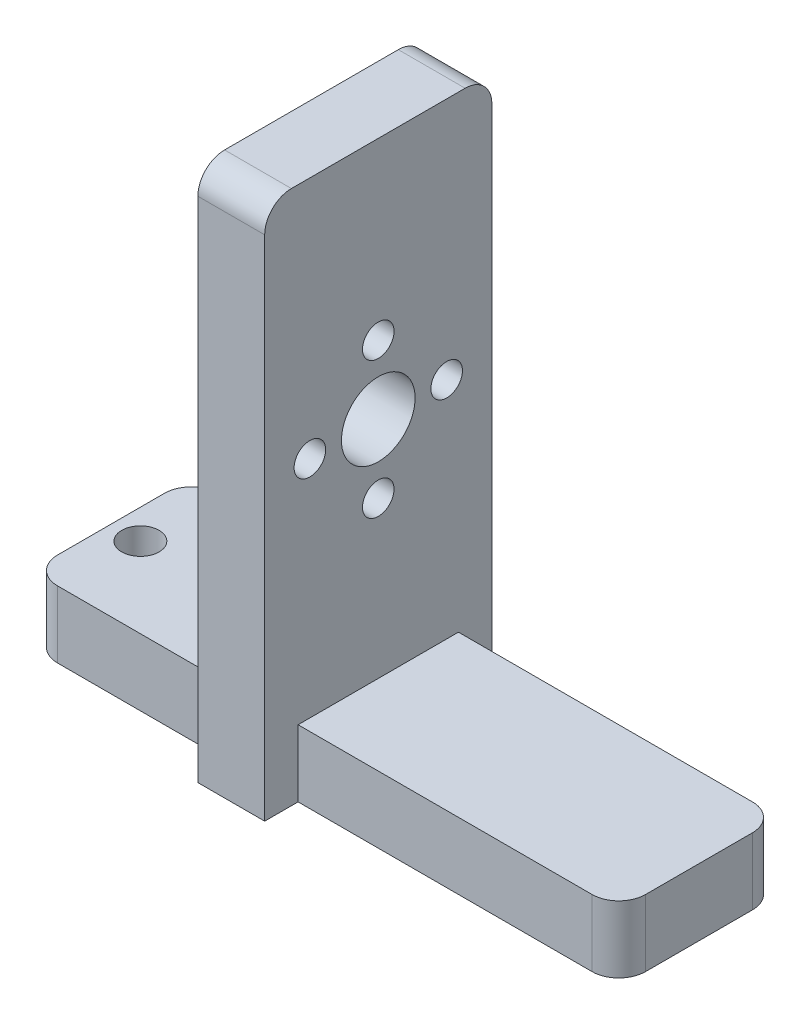
SolidWorks part; units mm, degrees
ref_plane "Front Plane" through (0, 0, 0) normal (0, 0, 1) x (1, 0, 0)
ref_plane "Top Plane" through (0, 0, 0) normal (0, 1, 0) x (1, 0, 0)
ref_plane "Right Plane" through (0, 0, 0) normal (1, 0, 0) x (0, 0, -1)
sketch "Sketch2" plane through (0, 0, 0) normal (0, 0, 1) x (1, 0, 0)
  line L0 (-27.94, 0) -> (27.94, 0)
  line L1 (27.94, 0) -> (27.94, 6.35)
  line L2 (27.94, 6.35) -> (-2.54, 6.35)
  line L3 (-2.54, 6.35) -> (-2.54, 50.8)
  line L4 (-2.54, 50.8) -> (-8.89, 50.8)
  line L5 (-8.89, 50.8) -> (-8.89, 6.35)
  line L6 (-8.89, 6.35) -> (-27.94, 6.35)
  line L7 (-27.94, 6.35) -> (-27.94, 0)
  dimension "D1" = 30.48
  dimension "D2" = 6.35
  dimension "D3" = 44.45
  dimension "D4" = 44.45
  dimension "D5" = 19.05
  dimension "D6" = 6.35
extrude "Boss-Extrude1" add sketch "Sketch2" along normal blind 15.24
sketch "Sketch5" plane through (-8.89, 0, 0) normal (-1, 0, 0) x (0, 0, 1)
  line L1 (15.24, 50.8) -> (0, 50.8) construction
  line L2 (0, 50.8) -> (0, 6.35) construction
  circle A1 centre (7.62, 27.686) radius 3.5
  dimension "D4" = 7
  dimension "D1" = 23.114
  dimension "D5" = 7.62
extrude "Cut-Extrude1" cut sketch "Sketch5" against normal blind 15.24
sketch "Sketch6" plane through (0, 6.35, 0) normal (0, 1, 0) x (1, 0, 0)
  line L0 (-8.89, 0) -> (-27.94, 0) construction
  line L1 (-27.94, -15.24) -> (-27.94, 0) construction
  circle A0 centre (-25.146, -7.62) radius 1.778
  circle A1 centre (-15.24, -7.62) radius 1.778
  dimension "D1" = 3.556
  dimension "D3" = 3.556
  dimension "D2" = 9.906
  dimension "D4" = 7.62
  dimension "D5" = 2.794
extrude "Cut-Extrude2" cut sketch "Sketch6" against normal blind 15.24
sketch "Sketch8" plane through (-8.89, 0, 0) normal (-1, 0, 0) x (0, 0, 1)
  line L1 (0, 50.8) -> (-3.175, 50.8)
  line L2 (0, 50.8) -> (0, 0)
  line L3 (0, 0) -> (-3.175, 0)
  line L4 (-3.175, 50.8) -> (-3.175, 0)
  line L5 (15.24, 50.8) -> (18.415, 50.8)
  line L6 (15.24, 50.8) -> (15.24, 0)
  line L7 (15.24, 0) -> (18.415, 0)
  line L8 (18.415, 50.8) -> (18.415, 0)
  dimension "D1" = 3.175
  dimension "D2" = 3.175
extrude "Boss-Extrude2" add sketch "Sketch8" against normal blind 6.35
sketch "Sketch7" plane through (-8.89, 0, 0) normal (-1, 0, 0) x (0, 0, 1)
  line L0 (15.24, 0) -> (15.24, 6.35) construction
  circle A0 centre (7.62, 34.186) radius 1.5
  circle A1 centre (7.62, 27.686) radius 3.5 construction
  dimension "D1" = 3
  dimension "D2" = 7.62
  dimension "D3" = 6.5
extrude "Cut-Extrude3" cut sketch "Sketch7" against normal blind 6.35
pattern_circular "CirPattern1" count 4 over 360 about axis through (0, 27.686, 7.62) along (1, 0, 0) of "Cut-Extrude3"
fillet "Fillet1" radius 2.54 6 edges at (27.94, 3.175, 15.24) (27.94, 3.175, 0) (-27.94, 3.175, 15.24) (-27.94, 3.175, 0) (-5.715, 50.8, 18.415) (-5.715, 50.8, -3.175)
